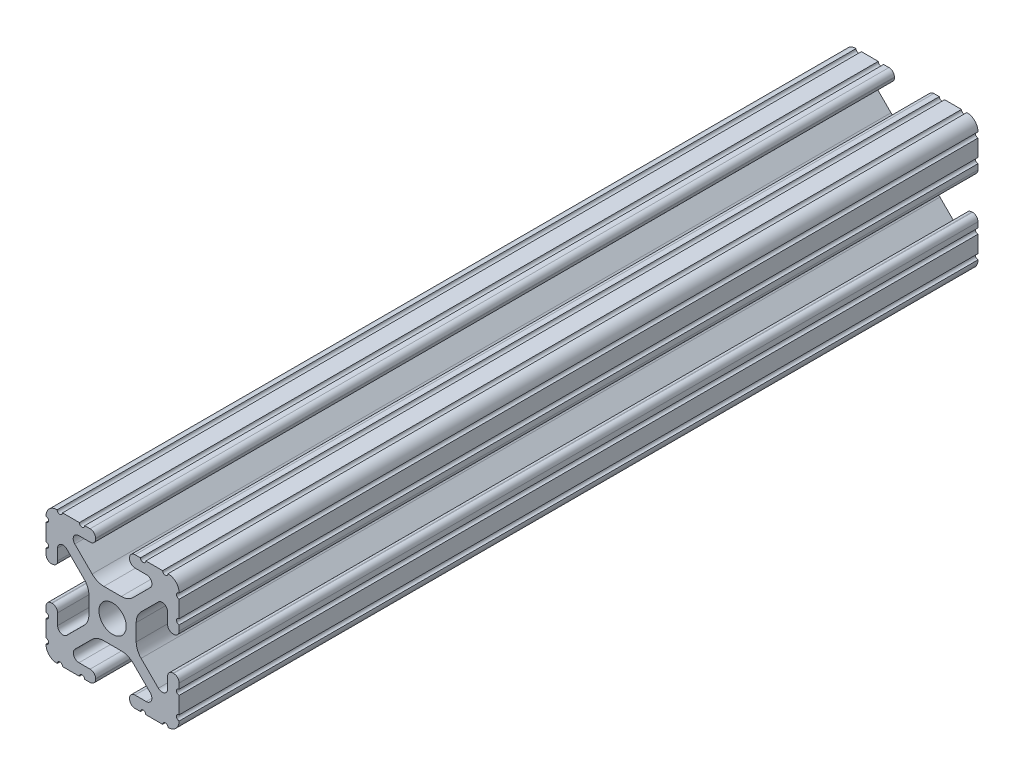
SolidWorks part; units mm, degrees
ref_plane "Front Plane" through (0, 0, 0) normal (0, 0, 1) x (1, 0, 0)
ref_plane "Top Plane" through (0, 0, 0) normal (0, 1, 0) x (1, 0, 0)
ref_plane "Right Plane" through (0, 0, 0) normal (1, 0, 0) x (0, 0, -1)
sketch "Sketch1" plane through (0, 0, 0) normal (0, 0, 1) x (1, 0, 0)
  line L88 (-7.1797, -8.6452) -> (-3.9523, -5.4237)
  line L89 (-1.7093, -4.4958) -> (1.7093, -4.4958)
  line L90 (3.9523, -5.4237) -> (7.1797, -8.6452)
  line L91 (6.4164, -10.4902) -> (4.2875, -10.4902)
  line L92 (3.2385, -11.5392) -> (3.2385, -11.651)
  line L93 (4.2875, -12.7) -> (5.3171, -12.7)
  line L94 (6.3331, -12.7) -> (9.5504, -12.7)
  line L95 (12.7, -9.5504) -> (12.7, -6.3331)
  line L96 (12.7, -5.3171) -> (12.7, -4.2875)
  line L97 (11.651, -3.2385) -> (11.5392, -3.2385)
  line L98 (10.4902, -4.2875) -> (10.4902, -6.4021)
  line L99 (8.7371, -7.1294) -> (5.441, -3.8408)
  line L100 (4.5085, -1.5932) -> (4.5085, 1.5932)
  line L101 (5.441, 3.8408) -> (8.7371, 7.1294)
  line L102 (10.4902, 6.4021) -> (10.4902, 4.2875)
  line L103 (11.5392, 3.2385) -> (11.651, 3.2385)
  line L104 (12.7, 4.2875) -> (12.7, 5.3171)
  line L105 (12.7, 6.3331) -> (12.7, 9.5504)
  line L106 (9.5504, 12.7) -> (6.3331, 12.7)
  line L107 (5.3171, 12.7) -> (4.2875, 12.7)
  line L108 (3.2385, 11.651) -> (3.2385, 11.5392)
  line L109 (4.2875, 10.4902) -> (6.4768, 10.4902)
  line L110 (7.207, 8.7244) -> (3.8983, 5.4232)
  line L111 (1.6558, 4.4958) -> (-1.6558, 4.4958)
  line L112 (-3.8983, 5.4232) -> (-7.207, 8.7244)
  line L113 (-6.4768, 10.4902) -> (-4.2875, 10.4902)
  line L114 (-3.2385, 11.5392) -> (-3.2385, 11.651)
  line L115 (-4.2875, 12.7) -> (-5.3171, 12.7)
  line L116 (-6.3331, 12.7) -> (-9.5504, 12.7)
  line L117 (-12.7, 9.5504) -> (-12.7, 6.3331)
  line L118 (-12.7, 5.3171) -> (-12.7, 4.2875)
  line L119 (-11.651, 3.2385) -> (-11.5392, 3.2385)
  line L120 (-10.4902, 4.2875) -> (-10.4902, 6.4021)
  line L121 (-8.7371, 7.1294) -> (-5.441, 3.8408)
  line L122 (-4.5085, 1.5932) -> (-4.5085, -1.5932)
  line L123 (-5.441, -3.8408) -> (-8.7371, -7.1294)
  line L124 (-10.4902, -6.4021) -> (-10.4902, -4.2875)
  line L125 (-11.5392, -3.2385) -> (-11.651, -3.2385)
  line L126 (-12.7, -4.2875) -> (-12.7, -5.3171)
  line L127 (-12.7, -6.3331) -> (-12.7, -9.5504)
  line L128 (-9.5504, -12.7) -> (-6.3331, -12.7)
  line L129 (-5.3171, -12.7) -> (-4.2875, -12.7)
  line L130 (-3.2385, -11.651) -> (-3.2385, -11.5392)
  line L131 (-4.2875, -10.4902) -> (-6.4164, -10.4902)
  circle A1 centre (0, 0) radius 2.6035
  arc A104 (-7.1797, -8.6452) -> (-6.4164, -10.4902) centre (-6.4164, -9.4098) ccw
  arc A105 (-1.7093, -4.4958) -> (-3.9523, -5.4237) centre (-1.7093, -7.6708) ccw
  arc A106 (3.9523, -5.4237) -> (1.7093, -4.4958) centre (1.7093, -7.6708) ccw
  arc A107 (6.4164, -10.4902) -> (7.1797, -8.6452) centre (6.4164, -9.4098) ccw
  arc A108 (4.2875, -10.4902) -> (3.2385, -11.5392) centre (4.2875, -11.5392) ccw
  arc A109 (3.2385, -11.651) -> (4.2875, -12.7) centre (4.2875, -11.651) ccw
  arc A110 (6.3331, -12.7) -> (5.3171, -12.7) centre (5.8251, -12.7) ccw
  arc A111 (10.5664, -12.6998) -> (9.5504, -12.7) centre (10.0584, -12.7) ccw
  arc A112 (10.5664, -12.6998) -> (12.6998, -10.5664) centre (10.5918, -10.5918) ccw
  arc A113 (12.7, -9.5504) -> (12.6998, -10.5664) centre (12.7, -10.0584) ccw
  arc A114 (12.7, -5.3171) -> (12.7, -6.3331) centre (12.7, -5.8251) ccw
  arc A115 (12.7, -4.2875) -> (11.651, -3.2385) centre (11.651, -4.2875) ccw
  arc A116 (11.5392, -3.2385) -> (10.4902, -4.2875) centre (11.5392, -4.2875) ccw
  arc A117 (8.7371, -7.1294) -> (10.4902, -6.4021) centre (9.4628, -6.4021) ccw
  arc A118 (4.5085, -1.5932) -> (5.441, -3.8408) centre (7.6835, -1.5932) ccw
  arc A119 (5.441, 3.8408) -> (4.5085, 1.5932) centre (7.6835, 1.5932) ccw
  arc A120 (10.4902, 6.4021) -> (8.7371, 7.1294) centre (9.4628, 6.4021) ccw
  arc A121 (10.4902, 4.2875) -> (11.5392, 3.2385) centre (11.5392, 4.2875) ccw
  arc A122 (11.651, 3.2385) -> (12.7, 4.2875) centre (11.651, 4.2875) ccw
  arc A123 (12.7, 6.3331) -> (12.7, 5.3171) centre (12.7, 5.8251) ccw
  arc A124 (12.6998, 10.5664) -> (12.7, 9.5504) centre (12.7, 10.0584) ccw
  arc A125 (12.6998, 10.5664) -> (10.5664, 12.6998) centre (10.5918, 10.5918) ccw
  arc A126 (9.5504, 12.7) -> (10.5664, 12.6998) centre (10.0584, 12.7) ccw
  arc A127 (5.3171, 12.7) -> (6.3331, 12.7) centre (5.8251, 12.7) ccw
  arc A128 (4.2875, 12.7) -> (3.2385, 11.651) centre (4.2875, 11.651) ccw
  arc A129 (3.2385, 11.5392) -> (4.2875, 10.4902) centre (4.2875, 11.5392) ccw
  arc A130 (7.207, 8.7244) -> (6.4768, 10.4902) centre (6.4768, 9.4563) ccw
  arc A131 (1.6558, 4.4958) -> (3.8983, 5.4232) centre (1.6558, 7.6708) ccw
  arc A132 (-3.8983, 5.4232) -> (-1.6558, 4.4958) centre (-1.6558, 7.6708) ccw
  arc A133 (-6.4768, 10.4902) -> (-7.207, 8.7244) centre (-6.4768, 9.4563) ccw
  arc A134 (-4.2875, 10.4902) -> (-3.2385, 11.5392) centre (-4.2875, 11.5392) ccw
  arc A135 (-3.2385, 11.651) -> (-4.2875, 12.7) centre (-4.2875, 11.651) ccw
  arc A136 (-6.3331, 12.7) -> (-5.3171, 12.7) centre (-5.8251, 12.7) ccw
  arc A137 (-10.5664, 12.6998) -> (-9.5504, 12.7) centre (-10.0584, 12.7) ccw
  arc A138 (-10.5664, 12.6998) -> (-12.6998, 10.5664) centre (-10.5918, 10.5918) ccw
  arc A139 (-12.7, 9.5504) -> (-12.6998, 10.5664) centre (-12.7, 10.0584) ccw
  arc A140 (-12.7, 5.3171) -> (-12.7, 6.3331) centre (-12.7, 5.8251) ccw
  arc A141 (-12.7, 4.2875) -> (-11.651, 3.2385) centre (-11.651, 4.2875) ccw
  arc A142 (-11.5392, 3.2385) -> (-10.4902, 4.2875) centre (-11.5392, 4.2875) ccw
  arc A143 (-8.7371, 7.1294) -> (-10.4902, 6.4021) centre (-9.4628, 6.4021) ccw
  arc A144 (-4.5085, 1.5932) -> (-5.441, 3.8408) centre (-7.6835, 1.5932) ccw
  arc A145 (-5.441, -3.8408) -> (-4.5085, -1.5932) centre (-7.6835, -1.5932) ccw
  arc A146 (-10.4902, -6.4021) -> (-8.7371, -7.1294) centre (-9.4628, -6.4021) ccw
  arc A147 (-10.4902, -4.2875) -> (-11.5392, -3.2385) centre (-11.5392, -4.2875) ccw
  arc A148 (-11.651, -3.2385) -> (-12.7, -4.2875) centre (-11.651, -4.2875) ccw
  arc A149 (-12.7, -6.3331) -> (-12.7, -5.3171) centre (-12.7, -5.8251) ccw
  arc A150 (-12.6998, -10.5664) -> (-12.7, -9.5504) centre (-12.7, -10.0584) ccw
  arc A151 (-12.6998, -10.5664) -> (-10.5664, -12.6998) centre (-10.5918, -10.5918) ccw
  arc A152 (-9.5504, -12.7) -> (-10.5664, -12.6998) centre (-10.0584, -12.7) ccw
  arc A153 (-5.3171, -12.7) -> (-6.3331, -12.7) centre (-5.8251, -12.7) ccw
  arc A154 (-4.2875, -12.7) -> (-3.2385, -11.651) centre (-4.2875, -11.651) ccw
  arc A155 (-3.2385, -11.5392) -> (-4.2875, -10.4902) centre (-4.2875, -11.5392) ccw
extrude "Boss-Extrude1" add sketch "Sketch1" along normal mid plane 152.4
